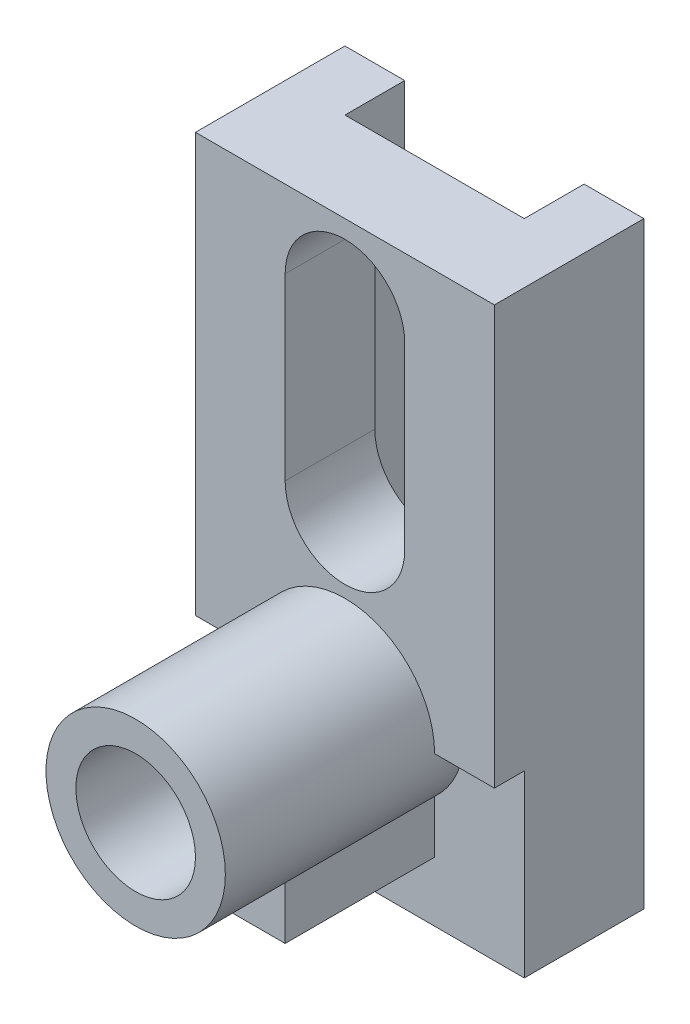
SolidWorks part; units mm, degrees
ref_plane "Ön Düzlem" through (0, 0, 0) normal (0, 0, 1) x (1, 0, 0)
ref_plane "Üst Düzlem" through (0, 0, 0) normal (0, 1, 0) x (1, 0, 0)
ref_plane "Sağ Düzlem" through (0, 0, 0) normal (1, 0, 0) x (0, 0, -1)
sketch "Çizim1" plane through (0, 0, 0) normal (0, 0, 1) x (1, 0, 0)
  line L1 (0, 0) -> (50, 0)
  line L2 (0, 0) -> (0, 100)
  line L3 (0, 100) -> (50, 100)
  line L4 (50, 0) -> (50, 100)
  dimension "D1" = 100
  dimension "D2" = 50
extrude "Yükseklik-Ekstrüzyon1" add sketch "Çizim1" along normal blind 60
sketch "Çizim2" plane through (0, 0, 60) normal (0, 0, 1) x (1, 0, 0)
  line L0 (0, 100) -> (0, 0) construction
  line L5 (0, 30) -> (10, 30)
  line L6 (0, 30) -> (0, 100)
  line L7 (0, 100) -> (50, 100)
  line L8 (50, 30) -> (50, 100)
  line L10 (50, 30) -> (40, 30)
  line L11 (10, 30) -> (40, 30) construction
  circle A0 centre (25, 30) radius 15
  circle A1 centre (25, 30) radius 10
  line M6 (0, 100) -> (0, 0)
  line M8 (50, 0) -> (50, 100)
  line M9 (50, 100) -> (0, 100)
  dimension "D2" = 20
  dimension "D1" = 30
  dimension "D3" = 10
  dimension "D4" = 10
extrude "Kes-Ekstrüzyon2" cut sketch "Çizim2" against normal blind 35 contours A0 L10 L5 M8 M9 M6 | L11 A1 | A1 L11
sketch "Çizim3" plane through (0, 0, 25) normal (0, 0, 1) x (1, 0, 0)
  line L0 (25, 57) -> (25, 87) construction
  line L1 (15, 57) -> (15, 87)
  line L2 (35, 57) -> (35, 87)
  line L4 (50, 30) -> (50, 100) construction
  arc A0 (15, 57) -> (35, 57) centre (25, 57) ccw
  arc A1 (35, 87) -> (15, 87) centre (25, 87) ccw
  arc A3 (40, 30) -> (10, 30) centre (25, 30) ccw construction
  circle A4 centre (25, 30) radius 10
  point P2 (25, 72)
  point P12 (25, 47)
  dimension "D1" = 10
  dimension "D2" = 17
  dimension "D3" = 30
  dimension "D4" = 15
extrude "Kes-Ekstrüzyon3" cut sketch "Çizim3" against normal blind 35
sketch "Çizim5" plane through (0, 0, 60) normal (0, 0, 1) x (1, 0, 0)
  line L0 (25, 10) -> (25, 30) construction
  line L1 (15, 10) -> (35, 10)
  line L2 (15, 10) -> (15, 18.8197)
  line L3 (35, 10) -> (35, 18.8197)
  line L4 (0, 0) -> (50, 0) construction
  line L5 (0, 30) -> (10, 30)
  line L6 (0, 30) -> (0, 0)
  line L7 (0, 0) -> (50, 0)
  line L8 (50, 0) -> (50, 30)
  circle A1 centre (25, 30) radius 15
  point P0 (25, 15.9276)
  dimension "D3" = 30
  dimension "D1" = 20
  dimension "D2" = 10
extrude "Kes-Ekstrüzyon4" cut sketch "Çizim5" against normal blind 40
sketch "Çizim6" plane through (0, 0, 60) normal (0, 0, 1) x (1, 0, 0)
  line L0 (15, 18.8197) -> (15, 10)
  line L1 (15, 10) -> (35, 10)
  line L2 (35, 10) -> (35, 18.8197)
  arc A0 (15, 18.8197) -> (35, 18.8197) centre (25, 30) ccw
extrude "Kes-Ekstrüzyon5" cut sketch "Çizim6" against normal blind 15
sketch "Çizim7" plane through (0, 10, 0) normal (0, -1, 0) x (1, 0, 0)
  line L0 (0, 20) -> (50, 20) construction
  line L1 (15, 45) -> (35, 45) construction
  circle A0 centre (25, 35) radius 5
  point P6 (0, 0)
  point P7 (25, 45)
  dimension "D1" = 15
  dimension "D2" = 10
extrude "Kes-Ekstrüzyon6" cut sketch "Çizim7" against normal blind 8
sketch "Çizim8" plane through (0, 0, 0) normal (0, -1, 0) x (1, 0, 0)
  line L0 (0, 0) -> (50, 0) construction
  line L1 (10, 0) -> (40, 0)
  line L2 (10, 0) -> (10, 10)
  line L3 (10, 10) -> (40, 10)
  line L4 (40, 0) -> (40, 10)
  line L5 (50, 20) -> (50, 0) construction
  line L6 (0, 20) -> (0, 0) construction
  dimension "D1" = 10
  dimension "D2" = 10
  dimension "D3" = 10
extrude "Kes-Ekstrüzyon7" cut sketch "Çizim8" against normal through all
